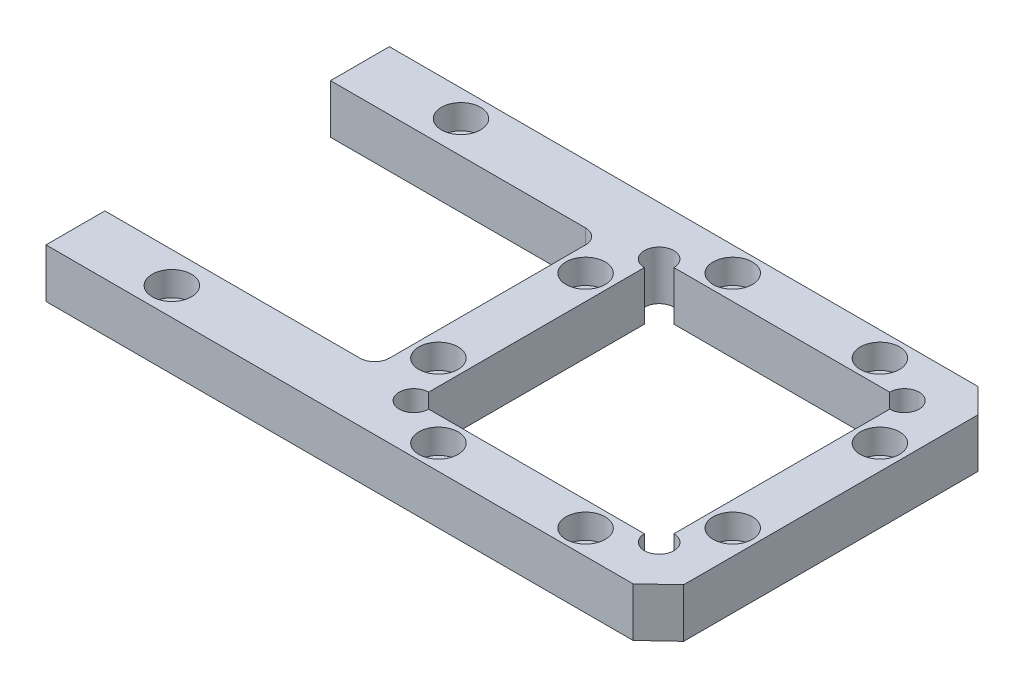
SolidWorks part; units mm, degrees
ref_plane "Front Plane" through (0, 0, 0) normal (0, 0, 1) x (1, 0, 0)
ref_plane "Top Plane" through (0, 0, 0) normal (0, 1, 0) x (1, 0, 0)
ref_plane "Right Plane" through (0, 0, 0) normal (1, 0, 0) x (0, 0, -1)
sketch "Sketch3" plane through (0, 0, 0) normal (0, 1, 0) x (1, 0, 0)
  line L0 (0, 0) -> (0, 70)
  line L1 (0, 70) -> (120, 70)
  line L2 (120, 70) -> (125, 65)
  line L3 (125, 65) -> (125, 5)
  line L4 (125, 5) -> (119.6667, 0)
  line L5 (119.6667, 0) -> (0, 0)
  point P3 (125, 35)
  point P8 (0, 35)
  dimension "D1" = 70
  dimension "D2" = 120
  dimension "D3" = 5
  dimension "D4" = 60
extrude "Boss-Extrude1" add sketch "Sketch3" along normal blind 10
sketch "Sketch4" plane through (0, 10, 0) normal (0, 1, 0) x (1, 0, 0)
  line L0 (0, 70) -> (0, 0) construction
  line L1 (0, 58) -> (55, 58)
  line L2 (0, 58) -> (0, 12)
  line L3 (0, 12) -> (55, 12)
  line L4 (55, 58) -> (55, 12)
  line L5 (120, 70) -> (0, 70) construction
  line L6 (0, 0) -> (119.6667, 0) construction
  dimension "D1" = 12
  dimension "D2" = 12
  dimension "D3" = 55
extrude "Cut-Extrude1" cut sketch "Sketch4" against normal through all
sketch "Sketch5" plane through (0, 10, 0) normal (0, 1, 0) x (1, 0, 0)
  line L0 (125, 5) -> (125, 65) construction
  line L1 (65, 60) -> (115, 60)
  line L2 (65, 60) -> (65, 10)
  line L3 (65, 10) -> (115, 10)
  line L4 (115, 60) -> (115, 10)
  line L5 (120, 70) -> (0, 70) construction
  line L6 (0, 0) -> (119.6667, 0) construction
  line L7 (55, 12) -> (55, 58) construction
  circle A0 centre (115, 60) radius 3
  circle A1 centre (115, 10) radius 3
  circle A2 centre (65, 10) radius 3
  circle A3 centre (65, 60) radius 3
  dimension "D5" = 6
  dimension "D1" = 10
  dimension "D2" = 10
  dimension "D3" = 10
  dimension "D4" = 10
extrude "Cut-Extrude2" cut sketch "Sketch5" against normal through all contours A3 L2 A2 L3 A1 L4 A0 L1 | L1 A3 L2 | L2 A3 L1 | L4 A0 L1 | L1 A0 L4 | L4 A1 L3 | L3 A1 L4 | L3 A2 L2 | L2 A2 L3
sketch "Sketch6" plane through (0, 10, 0) normal (0, 1, 0) x (1, 0, 0)
  line L0 (0, 70) -> (0, 58) construction
  circle A0 centre (20, 64.5978) radius 4
  circle A1 centre (20, 5.6585) radius 4
  point P6 (0, 0)
  dimension "D1" = 8
  dimension "D2" = 8
  dimension "D3" = 20
extrude "Cut-Extrude4" cut sketch "Sketch6" against normal blind 5
sketch "Sketch7" plane through (0, 5, 0) normal (0, 1, 0) x (1, 0, 0)
  circle A0 centre (20, 64.5978) radius 2.5
  circle A1 centre (20, 5.6585) radius 2.5
  dimension "D1" = 5
  dimension "D2" = 5
extrude "Cut-Extrude5" cut sketch "Sketch7" against normal through all
fillet "Fillet1" radius 3 2 edges at (55, 5, -12) (55, 5, -58)
sketch "Sketch8" plane through (0, 10, 0) normal (0, 1, 0) x (1, 0, 0)
  line L0 (125, 5) -> (125, 65) construction
  line L1 (0, 0) -> (119.6667, 0) construction
  line L2 (120, 70) -> (0, 70) construction
  line L3 (55, 15) -> (55, 55) construction
  line L4 (65, 57) -> (65, 13) construction
  circle A0 centre (120, 50) radius 4
  circle A1 centre (120, 20) radius 4
  circle A2 centre (105, 65) radius 4
  circle A3 centre (75, 65) radius 4
  circle A4 centre (75, 5) radius 4
  circle A5 centre (105, 5) radius 4
  circle A6 centre (60, 50) radius 4
  circle A7 centre (60, 20) radius 4
  point P14 (0, 0)
  point P17 (0, 0)
  point P20 (0, 0)
  point P27 (0, 0)
  point P28 (0, 0)
  dimension "D1" = 8
  dimension "D2" = 5
  dimension "D3" = 5
  dimension "D4" = 5
  dimension "D5" = 20
  dimension "D6" = 20
  dimension "D7" = 20
  dimension "D8" = 20
  dimension "D9" = 20
  dimension "D10" = 20
  dimension "D11" = 5
extrude "Cut-Extrude6" cut sketch "Sketch8" against normal blind 5
